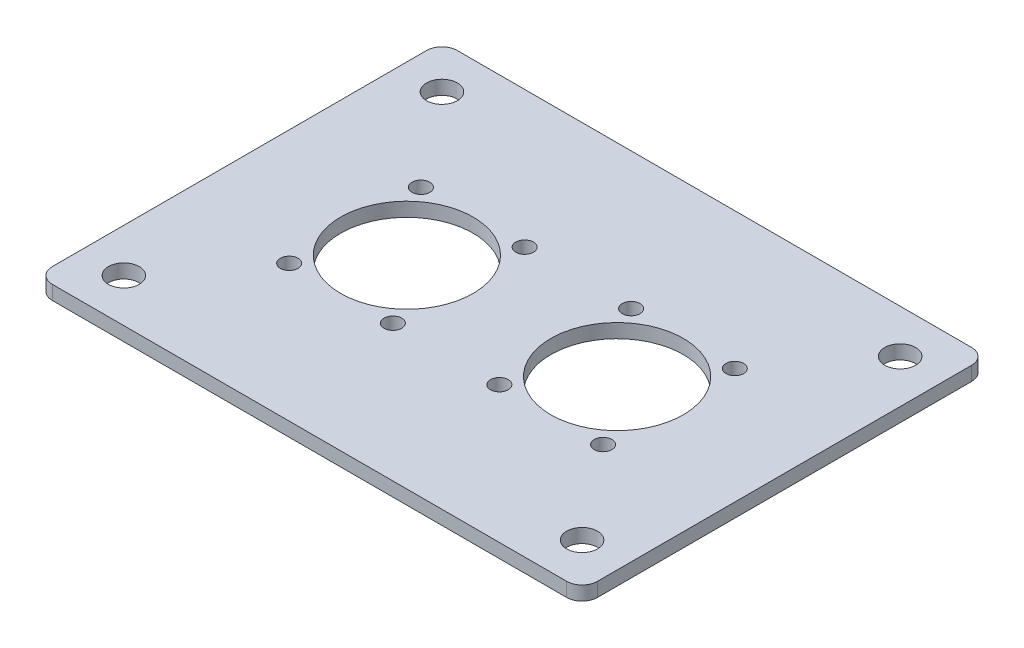
SolidWorks part; units mm, degrees
material "6061 Alloy"
ref_plane "Front" through (0, 0, 0) normal (0, 0, 1) x (1, 0, 0)
ref_plane "Top" through (0, 0, 0) normal (0, 1, 0) x (1, 0, 0)
ref_plane "Right" through (0, 0, 0) normal (1, 0, 0) x (0, 0, -1)
sketch "Sketch1" plane through (0, 0, 0) normal (0, 1, 0) x (1, 0, 0)
  line L1 (-46.609, -36.703) -> (46.609, -36.703)
  line L2 (-49.403, -33.909) -> (-49.403, 33.909)
  line L3 (-46.609, 36.703) -> (46.609, 36.703)
  line L4 (49.403, -33.909) -> (49.403, 33.909)
  line L5 (0, 36.703) -> (0, -36.703) construction
  line L6 (-49.403, 0) -> (49.403, 0) construction
  arc A0 (46.609, 36.703) -> (49.403, 33.909) centre (46.609, 33.909) cw
  arc A1 (46.609, -36.703) -> (49.403, -33.909) centre (46.609, -33.909) ccw
  arc A2 (-46.609, -36.703) -> (-49.403, -33.909) centre (-46.609, -33.909) cw
  arc A3 (-49.403, 33.909) -> (-46.609, 36.703) centre (-46.609, 33.909) cw
  circle A4 centre (-19.05, 0) radius 12.0015
  circle A5 centre (19.05, 0) radius 12.0015
  circle A6 centre (-41.529, 28.829) radius 2.794
  circle A7 centre (-28.448, -11.938) radius 1.6002
  circle A8 centre (-9.652, -11.938) radius 1.6002
  circle A9 centre (-9.652, 11.938) radius 1.6002
  circle A10 centre (-28.448, 11.938) radius 1.6002
  circle A11 centre (9.652, 11.938) radius 1.6002
  circle A12 centre (28.448, 11.938) radius 1.6002
  circle A13 centre (28.448, -11.938) radius 1.6002
  circle A14 centre (9.652, -11.938) radius 1.6002
  circle A15 centre (41.529, 28.829) radius 2.794
  circle A16 centre (41.529, -28.829) radius 2.794
  circle A17 centre (-41.529, -28.829) radius 2.794
  point P0 (0, 0)
  dimension "D3" = 2.794
  dimension "D5" = 24.003
  dimension "D6" = 5.588
  dimension "D10" = 3.2004
  dimension "D13" = 5.08
  dimension "D1" = 73.406
  dimension "D2" = 98.806
  dimension "D4" = 38.1
  dimension "D7" = 19.05
  dimension "D8" = 9.398
  dimension "D9" = 11.938
  dimension "D14" = 5.08
  dimension "D16" = 5.08
  dimension "D17" = 5.08
  dimension "D18" = 5.08
  dimension "D19" = 5.08
  dimension "D20" = 5.08
  dimension "D21" = 5.08
  dimension "D11" = 2
  dimension "D12" = 2
  dimension "D15" = 2
extrude "Boss-Extrude1" add sketch "Sketch1" along normal blind 2.54
